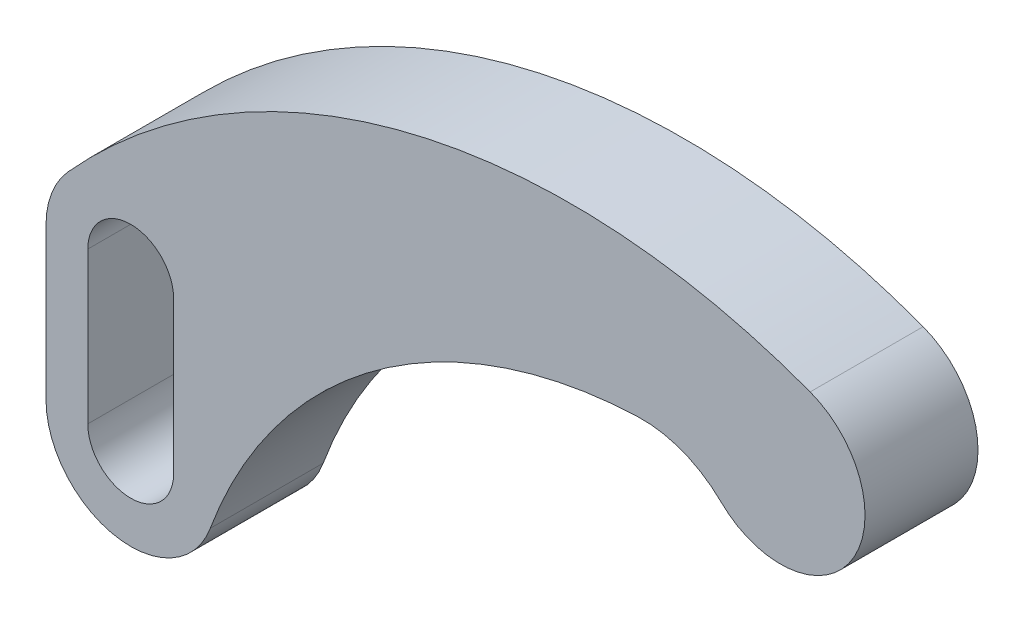
SolidWorks part; units mm, degrees
ref_plane "Front Plane" through (0, 0, 0) normal (0, 0, 1) x (1, 0, 0)
ref_plane "Top Plane" through (0, 0, 0) normal (0, 1, 0) x (1, 0, 0)
ref_plane "Right Plane" through (0, 0, 0) normal (1, 0, 0) x (0, 0, -1)
sketch "Sketch1" plane through (0, 0, 0) normal (0, 0, 1) x (1, 0, 0)
  line L0 (-136.398, -35.56) -> (-136.398, -69.596)
  line L1 (-155.702, -35.56) -> (-155.702, -69.596)
  line L2 (-165.1, -35.56) -> (-165.1, -69.596)
  arc A0 (-13.3322, -13.6071) -> (6.7095, 17.8293) centre (0, 0) ccw
  arc A1 (-165.1, -69.596) -> (-128.1696, -76.1681) centre (-146.05, -69.596) ccw
  arc A2 (-155.702, -69.596) -> (-136.398, -69.596) centre (-146.05, -69.596) ccw
  arc A3 (-136.398, -35.56) -> (-155.702, -35.56) centre (-146.05, -35.56) ccw
  arc A5 (-160.2048, -22.8107) -> (-165.1, -35.56) centre (-146.05, -35.56) ccw
  arc A6 (-13.3322, -13.6071) -> (-32.0677, -6.3681) centre (-31.1085, -31.75) ccw
  arc A7 (-32.0677, -6.3681) -> (-128.1696, -76.1681) centre (-28.0392, -112.972) ccw
  arc A8 (6.7095, 17.8293) -> (-160.2048, -22.8107) centre (-46.9667, -124.8053) ccw
  dimension "D1" = 146.05
  dimension "D3" = 34.036
  dimension "D4" = 106.68
  dimension "D5" = 19.05
  dimension "D6" = 25.4
  dimension "D7" = 31.75
  dimension "D8" = 19.05
  dimension "D9" = 152.4
  dimension "D10" = 9.652
  dimension "D2" = 69.596
extrude "Boss-Extrude1" add sketch "Sketch1" along normal blind 25.4
